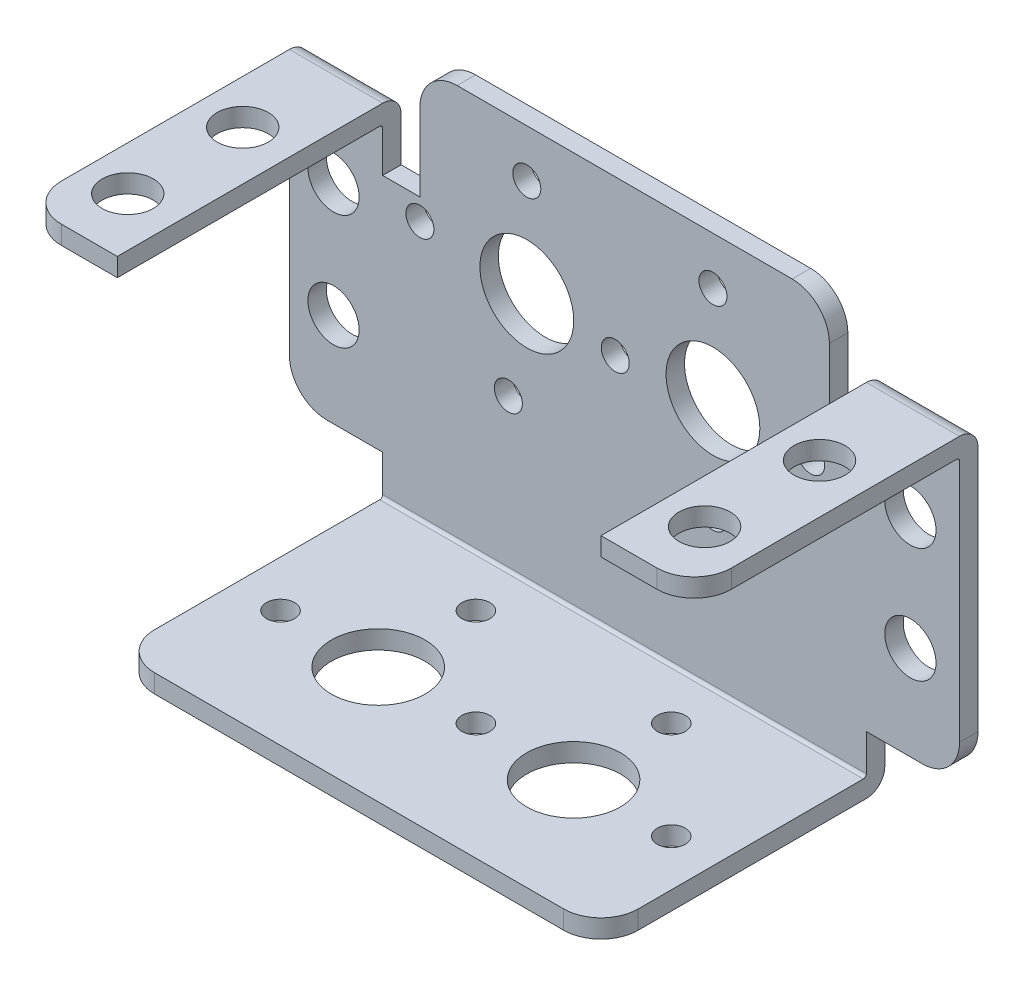
SolidWorks part; units mm, degrees
ref_plane "Front Plane" through (0, 0, 0) normal (0, 0, 1) x (1, 0, 0)
ref_plane "Top Plane" through (0, 0, 0) normal (0, 1, 0) x (1, 0, 0)
ref_plane "Right Plane" through (0, 0, 0) normal (1, 0, 0) x (0, 0, -1)
sketch "Sketch1" plane through (0, 0, 0) normal (0, 0, 1) x (1, 0, 0)
  line L0 (11.9126, 30.734) -> (11.9126, 32.042)
  line L1 (8.7376, 0) -> (49.9872, 0)
  line L2 (0.7874, 8.128) -> (0.7874, 30.734)
  line L3 (0.7874, 30.734) -> (8.7376, 30.734)
  line L4 (57.9374, 8.128) -> (57.9374, 30.734)
  line L5 (15.0876, 35.217) -> (43.6626, 35.217)
  line L6 (46.8376, 32.042) -> (46.8376, 30.734)
  line L7 (49.9872, 30.734) -> (57.9374, 30.734)
  line L8 (3.9624, 4.953) -> (8.7376, 4.953)
  line L9 (8.7376, 4.953) -> (8.7376, 0)
  line L10 (49.9872, 0) -> (49.9872, 4.953)
  line L11 (49.9872, 4.953) -> (54.7624, 4.953)
  line L12 (11.9126, 30.734) -> (11.9126, 25.4)
  line L13 (11.9126, 25.4) -> (8.7376, 25.4)
  line L14 (8.7376, 25.4) -> (8.7376, 30.734)
  line L15 (46.8376, 30.734) -> (46.8376, 25.4)
  line L16 (46.8376, 25.4) -> (49.9872, 25.4)
  line L17 (49.9872, 25.4) -> (49.9872, 30.734)
  arc A0 (11.9126, 32.042) -> (15.0876, 35.217) centre (15.0876, 32.042) cw
  arc A1 (43.6626, 35.217) -> (46.8376, 32.042) centre (43.6626, 32.042) cw
  arc A2 (3.9624, 4.953) -> (0.7874, 8.128) centre (3.9624, 8.128) cw
  arc A3 (54.7624, 4.953) -> (57.9374, 8.128) centre (54.7624, 8.128) ccw
  circle A4 centre (21.0312, 22.8092) radius 4.0005
  circle A5 centre (21.0312, 22.8092) radius 8.3312 construction
  circle A6 centre (21.0312, 31.1404) radius 1.1938
  circle A7 centre (28.575, 22.0218) radius 1.1938
  circle A8 centre (19.4564, 14.478) radius 1.1938
  circle A9 centre (11.9126, 23.5966) radius 1.1938
  circle A10 centre (36.9062, 31.1404) radius 1.1938
  circle A11 centre (45.2374, 22.8092) radius 1.1938
  circle A12 centre (36.9062, 22.8092) radius 4.0005
  circle A13 centre (36.9062, 14.478) radius 1.1938
  circle A14 centre (4.5466, 22.7838) radius 2.1844
  circle A15 centre (4.5466, 12.9794) radius 2.1844
  circle A16 centre (53.7464, 22.7838) radius 2.1844
  circle A17 centre (53.7464, 12.9794) radius 2.1844
  dimension "D5" = 3.175
  dimension "D1" = 3.175
  dimension "D10" = 8.001
  dimension "D11" = 16.6624
  dimension "D12" = 2.3876
  dimension "D15" = 4.3688
  dimension "D16" = 4.3688
  dimension "D18" = 4.3688
  dimension "D20" = 4.3688
  dimension "D2" = 22.8092
  dimension "D3" = 11.1252
  dimension "D4" = 46.0502
  dimension "D6" = 4.953
  dimension "D7" = 4.953
  dimension "D8" = 7.9502
  dimension "D9" = 49.1998
  dimension "D13" = 20.2438
  dimension "D14" = 22.7838
  dimension "D17" = 12.9794
  dimension "D19" = 22.7838
  dimension "D21" = 7.9502
  dimension "D22" = 25.4
  dimension "D23" = 25.4
  dimension "D24" = 49.1998
  dimension "D25" = 3.7592
  dimension "D26" = 3.7592
  dimension "D27" = 52.959
  dimension "D28" = 12.9794
  dimension "D29" = 52.959
extrude "Extrude2" add sketch "Sketch1" along normal blind 1.5748
sketch "Sketch3" plane through (0, 0, 1.5748) normal (0, 0, 1) x (1, 0, 0)
  line L0 (8.7376, 25.4) -> (8.7376, 30.734) construction
  line L1 (0.7874, 30.734) -> (8.7376, 30.734)
  line L2 (0.7874, 30.734) -> (0.7874, 29.1592)
  line L3 (0.7874, 29.1592) -> (8.7376, 29.1592)
  line L4 (8.7376, 30.734) -> (8.7376, 29.1592)
  line L5 (8.7376, 4.953) -> (8.7376, 0) construction
  line L6 (8.7376, 1.5748) -> (49.9872, 1.5748)
  line L7 (8.7376, 1.5748) -> (8.7376, 0)
  line L8 (8.7376, 0) -> (49.9872, 0)
  line L9 (49.9872, 1.5748) -> (49.9872, 0)
  line L10 (57.9374, 8.128) -> (57.9374, 30.734) construction
  line L11 (49.9872, 30.734) -> (57.9374, 30.734)
  line L12 (49.9872, 30.734) -> (49.9872, 29.1592)
  line L13 (49.9872, 29.1592) -> (57.9374, 29.1592)
  line L14 (57.9374, 30.734) -> (57.9374, 29.1592)
  dimension "D1" = 1.5748
  dimension "D2" = 1.5748
extrude "Extrude3" add sketch "Sketch3" along normal blind 22.6314
fillet "Fillet1" radius 3.175 4 edges at (8.7376, 0.7874, 24.2062) (49.9872, 0.7874, 24.2062) (57.9374, 29.9466, 24.2062) (0.7874, 29.9466, 24.2062)
fillet "Fillet2" radius 1.5748 3 edges at (29.3624, 0, 0) (4.7625, 30.734, 0) (53.9623, 30.734, 0)
fillet "Fillet3" radius 0.254 3 edges at (29.3624, 1.5748, 1.5748) (4.7625, 29.1592, 1.5748) (53.9623, 29.1592, 1.5748)
sketch "Sketch4" plane through (0, 0, 0) normal (0, -1, 0) x (1, 0, 0)
  line L0 (49.9872, 0) -> (8.7376, 0) construction
  line L1 (0.7874, 21.0312) -> (0.7874, 1.8288) construction
  circle A0 centre (21.0312, 14.2494) radius 4.0005
  circle A1 centre (21.0312, 14.2494) radius 8.3312 construction
  circle A2 centre (12.7, 14.2494) radius 1.1938
  circle A3 centre (21.0312, 5.9182) radius 1.1938
  circle A4 centre (29.3624, 14.2494) radius 1.1938
  circle A5 centre (46.0248, 14.2494) radius 1.1938
  circle A6 centre (37.6936, 14.2494) radius 4.0005
  circle A7 centre (37.6936, 5.9182) radius 1.1938
  dimension "D1" = 14.2494
  dimension "D2" = 8.001
  dimension "D3" = 20.2438
extrude "Extrude4" cut sketch "Sketch4" against normal up to surface (1.5748 mm away) up to face at (29.3624, 1.5748, 15.9079)
sketch "Sketch5" plane through (0, 30.734, 0) normal (0, 1, 0) x (1, 0, 0)
  line L0 (0.7874, -21.0312) -> (0.7874, -1.5748) construction
  line L1 (43.6626, 0) -> (15.0876, 0) construction
  circle A0 centre (4.5466, -9.3218) radius 2.1844
  circle A1 centre (4.5466, -19.1262) radius 2.1844
  circle A2 centre (53.7464, -19.1262) radius 2.1844
  circle A3 centre (53.7464, -9.3218) radius 2.1844
  dimension "D1" = 4.3688
  dimension "D2" = 4.3688
  dimension "D3" = 3.7592
  dimension "D4" = 9.3218
  dimension "D5" = 19.1262
extrude "Extrude5" cut sketch "Sketch5" against normal up to surface (1.5748 mm away) up to face at (4.471, 29.1592, 14.7518)
